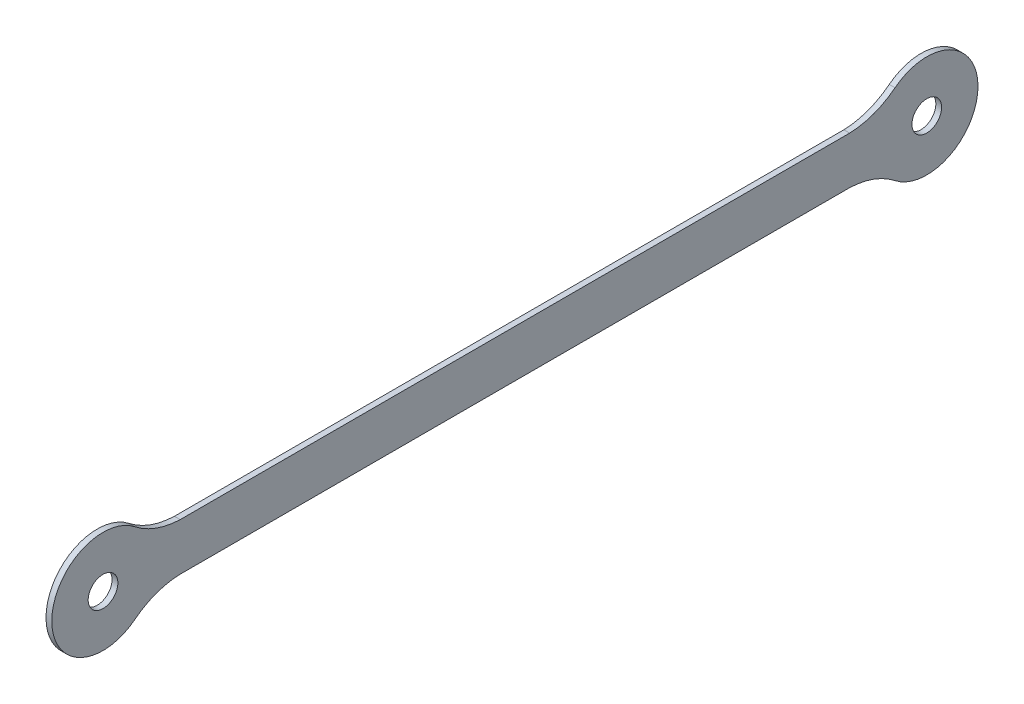
SolidWorks part; units mm, degrees
ref_plane "前基準面" through (0, 0, 0) normal (0, 0, 1) x (1, 0, 0)
ref_plane "上基準面" through (0, 0, 0) normal (0, 1, 0) x (1, 0, 0)
ref_plane "右基準面" through (0, 0, 0) normal (1, 0, 0) x (0, 0, -1)
sketch "草圖2" plane through (0, 0, 0) normal (1, 0, 0) x (0, 0, -1)
  line L0 (86.8673, 6.1363) -> (-86.8673, 6.1363)
  line L1 (86.8673, -6.1363) -> (-86.8673, -6.1363)
  line L2 (-106.89, 0) -> (106.89, 0) construction
  line L3 (0, 0) -> (0, -17.9832) construction
  arc A0 (98.6532, -10.4367) -> (98.6532, 10.4367) centre (106.89, 0) ccw
  arc A1 (-98.6532, 10.4367) -> (-98.6532, -10.4367) centre (-106.89, 0) ccw
  circle A2 centre (-106.89, 0) radius 3.85
  circle A3 centre (106.89, 0) radius 3.85
  arc A4 (-98.6532, 10.4367) -> (-86.8673, 6.1363) centre (-86.2339, 26.1728) ccw
  arc A5 (-98.6532, -10.4367) -> (-86.8673, -6.1363) centre (-86.2339, -26.1728) cw
  arc A6 (98.6532, -10.4367) -> (86.8673, -6.1363) centre (86.2339, -26.1728) ccw
  arc A7 (98.6532, 10.4367) -> (86.8673, 6.1363) centre (86.2339, 26.1728) cw
  point P11 (0, 6.1363)
  point P13 (0, -6.1363)
  point P16 (0, -6.1363)
  point P17 (0, 6.1363)
  dimension "D1" = 7.7
extrude "填料-伸長1" add sketch "草圖2" along normal blind 1.5
